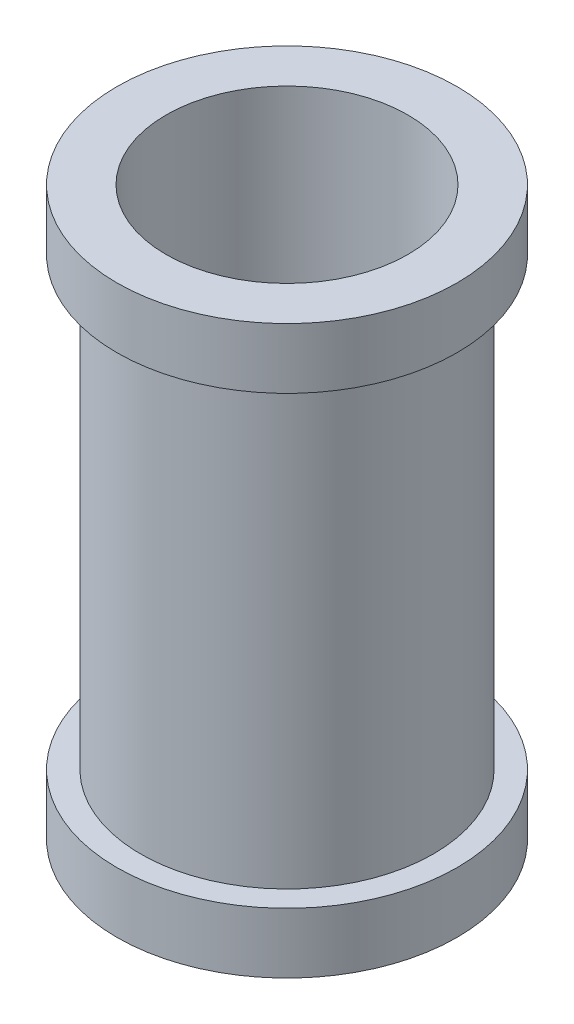
SolidWorks part; units mm, degrees
ref_plane "Front Plane" through (0, 0, 0) normal (0, 0, 1) x (1, 0, 0)
ref_plane "Top Plane" through (0, 0, 0) normal (0, 1, 0) x (1, 0, 0)
ref_plane "Right Plane" through (0, 0, 0) normal (1, 0, 0) x (0, 0, -1)
sketch "Sketch1" plane through (0, 0, 0) normal (0, 1, 0) x (1, 0, 0)
  circle A0 centre (0, 0) radius 20.32
  circle A1 centre (0, 0) radius 0.5
  circle A2 centre (0, 0) radius 24.6062
  dimension "D1" = 49.2125
  dimension "D2" = 40.64
extrude "Boss-Extrude1" add sketch "Sketch1" along normal blind 95.25 contours A2 A0
sketch "Sketch2" plane through (0, 95.25, 0) normal (0, 1, 0) x (1, 0, 0)
  circle A0 centre (0, 0) radius 28.575
  circle A1 centre (0, 0) radius 24.6063
  dimension "D1" = 57.15
extrude "Boss-Extrude2" add sketch "Sketch2" against normal up to surface (95.25 mm away) up to face at (0, 0, 20.32)
sketch "Sketch3" plane through (0, 0, 0) normal (0, 0, 1) x (1, 0, 0)
  line L0 (0, -3.1128) -> (0, 134.5942) construction
  line L1 (-28.575, 95.25) -> (-28.575, 0) construction
  line L2 (28.575, 10.16) -> (-28.575, 10.16)
  line L3 (28.575, 10.16) -> (28.575, 85.09)
  line L4 (28.575, 85.09) -> (-28.575, 85.09)
  line L5 (-28.575, 10.16) -> (-28.575, 85.09)
  line L6 (28.575, 10.16) -> (-28.575, 85.09) construction
  line L7 (28.575, 85.09) -> (-28.575, 10.16) construction
  point P1 (0, 47.625)
  dimension "D1" = 10.16
  dimension "D2" = 10.16
extrude "Cut-Extrude1" cut sketch "Sketch3" against normal through all both and the other way through all
sketch "Sketch4" plane through (0, 10.16, 0) normal (0, 1, 0) x (1, 0, 0)
  circle A0 centre (0, 0) radius 24.6062
  circle A1 centre (0, 0) radius 20.32
  dimension "D1" = 49.2125
extrude "Boss-Extrude3" add sketch "Sketch4" along normal up to surface (74.93 mm away) up to face at (-20.32, 85.09, 0)
